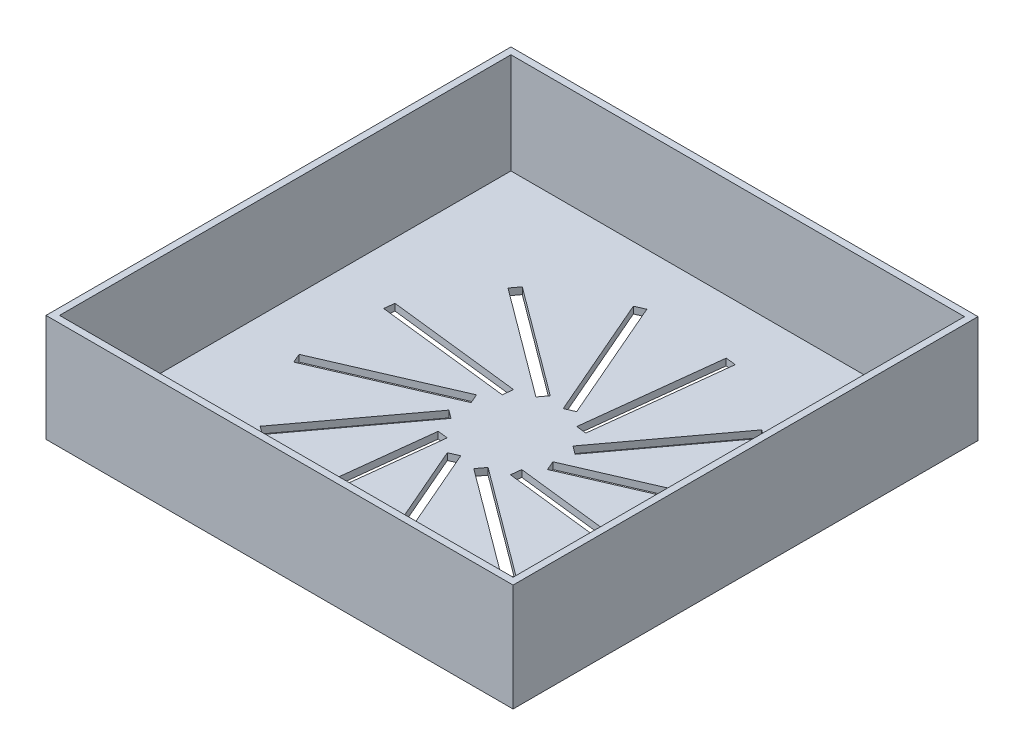
SolidWorks part; units mm, degrees
ref_plane "Front Plane" through (0, 0, 0) normal (0, 0, 1) x (1, 0, 0)
ref_plane "Top Plane" through (0, 0, 0) normal (0, 1, 0) x (1, 0, 0)
ref_plane "Right Plane" through (0, 0, 0) normal (1, 0, 0) x (0, 0, -1)
sketch "Sketch1" plane through (0, 0, 0) normal (0, 1, 0) x (1, 0, 0)
  line L1 (81.3084, 24.2428) -> (136.5534, 24.2428)
  line L2 (81.3084, 24.2428) -> (81.3084, -30.7482)
  line L3 (81.3084, -30.7482) -> (136.5534, -30.7482)
  line L4 (136.5534, 24.2428) -> (136.5534, -30.7482)
  dimension "D1" = 55.245
  dimension "D2" = 54.991
extrude "Boss-Extrude1" add sketch "Sketch1" along normal blind 12.7
sketch "Sketch2" plane through (0, 12.7, 0) normal (0, 1, 0) x (1, 0, 0)
  line L0 (81.3084, 24.2428) -> (81.3084, -30.7482) construction
  line L1 (135.7534, -29.9482) -> (82.1084, -29.9482)
  line L2 (135.7534, -29.9482) -> (135.7534, 23.4428)
  line L3 (135.7534, 23.4428) -> (82.1084, 23.4428)
  line L4 (82.1084, -29.9482) -> (82.1084, 23.4428)
  line L5 (136.5534, -30.7482) -> (136.5534, 24.2428) construction
  line L6 (136.5534, 24.2428) -> (81.3084, 24.2428) construction
  line L7 (81.3084, -30.7482) -> (136.5534, -30.7482) construction
  dimension "D1" = 0.8
  dimension "D2" = 0.8
  dimension "D3" = 0.8
  dimension "D4" = 0.8
extrude "Cut-Extrude1" cut sketch "Sketch2" against normal blind 11.9 contours L4 L3 L2 L1
sketch "Sketch3" plane through (0, 0.8, 0) normal (0, 1, 0) x (1, 0, 0)
  line L0 (108.9309, -999.2902) -> (108.9309, 49000.7098) construction
  line L1 (-891.3174, -3.2527) -> (49108.6826, -3.2527) construction
  line L5 (92.0152, 23.4428) -> (92.0152, -3.2527) construction
  line L6 (135.7534, 23.4428) -> (82.1084, 23.4428) construction
  line L7 (92.0152, -3.2527) -> (92.0152, -29.9482) construction
  line L8 (135.7534, -29.9482) -> (82.1084, -29.9482) construction
  line L9 (82.1084, 4.3934) -> (108.9309, 4.3934) construction
  line L10 (82.1084, -29.9482) -> (82.1084, 23.4428) construction
  line L11 (108.9309, 4.3934) -> (135.7534, 4.3934) construction
  line L12 (135.7534, -29.9482) -> (135.7534, 23.4428) construction
  line L13 (88.8111, 3.03) -> (104.6601, 1.2037)
  line L14 (88.8111, 3.03) -> (88.6724, 1.8263)
  line L15 (104.6601, 1.2037) -> (104.5214, 0)
  line L16 (88.6724, 1.8263) -> (104.5214, 0)
  line L17 (94.648, 12.2481) -> (107.4605, 2.742)
  line L18 (94.648, 12.2481) -> (93.926, 11.2751)
  line L19 (93.926, 11.2751) -> (106.7386, 1.7689)
  line L20 (107.4605, 2.742) -> (106.7386, 1.7689)
  line L21 (104.312, 17.3128) -> (110.6549, 2.674)
  line L22 (104.312, 17.3128) -> (103.2002, 16.8311)
  line L23 (103.2002, 16.8311) -> (109.5431, 2.1923)
  line L24 (110.6549, 2.674) -> (109.5431, 2.1923)
  line L25 (115.2136, 16.867) -> (113.3873, 1.018)
  line L26 (115.2136, 16.867) -> (114.0099, 17.0057)
  line L27 (114.0099, 17.0057) -> (112.1836, 1.1567)
  line L28 (113.3873, 1.018) -> (112.1836, 1.1567)
  line L29 (124.4317, 11.0301) -> (114.9256, -1.7824)
  line L30 (124.4317, 11.0301) -> (123.4586, 11.7521)
  line L31 (123.4586, 11.7521) -> (113.9525, -1.0604)
  line L32 (114.9256, -1.7824) -> (113.9525, -1.0604)
  line L33 (129.4964, 1.3662) -> (114.8576, -4.9767)
  line L34 (129.4964, 1.3662) -> (129.0147, 2.4779)
  line L35 (129.0147, 2.4779) -> (114.3759, -3.865)
  line L36 (114.8576, -4.9767) -> (114.3759, -3.865)
  line L37 (129.0506, -9.5354) -> (113.2016, -7.7091)
  line L38 (129.0506, -9.5354) -> (129.1893, -8.3318)
  line L39 (129.1893, -8.3318) -> (113.3403, -6.5055)
  line L40 (113.2016, -7.7091) -> (113.3403, -6.5055)
  line L41 (123.2137, -18.7536) -> (110.4012, -9.2475)
  line L42 (123.2137, -18.7536) -> (123.9357, -17.7805)
  line L43 (123.9357, -17.7805) -> (111.1232, -8.2744)
  line L44 (110.4012, -9.2475) -> (111.1232, -8.2744)
  line L45 (113.5498, -23.8183) -> (107.2069, -9.1795)
  line L46 (113.5498, -23.8183) -> (114.6615, -23.3366)
  line L47 (114.6615, -23.3366) -> (108.3186, -8.6978)
  line L48 (107.2069, -9.1795) -> (108.3186, -8.6978)
  line L49 (102.6482, -23.3725) -> (104.4744, -7.5234)
  line L50 (102.6482, -23.3725) -> (103.8518, -23.5112)
  line L51 (103.8518, -23.5112) -> (105.6781, -7.6621)
  line L52 (104.4744, -7.5234) -> (105.6781, -7.6621)
  line L53 (93.43, -17.5356) -> (102.9361, -4.7231)
  line L54 (93.43, -17.5356) -> (94.4031, -18.2576)
  line L55 (94.4031, -18.2576) -> (103.9092, -5.445)
  line L56 (102.9361, -4.7231) -> (103.9092, -5.445)
  line L57 (88.3653, -7.8716) -> (103.0041, -1.5287)
  line L58 (88.3653, -7.8716) -> (88.847, -8.9834)
  line L59 (88.847, -8.9834) -> (103.4858, -2.6405)
  line L60 (103.0041, -1.5287) -> (103.4858, -2.6405)
  point P15 (104.6601, 0)
  point P69 (108.9309, -3.2527)
  dimension "D1" = 12
extrude "Cut-Extrude2" cut sketch "Sketch3" against normal blind 11.9
